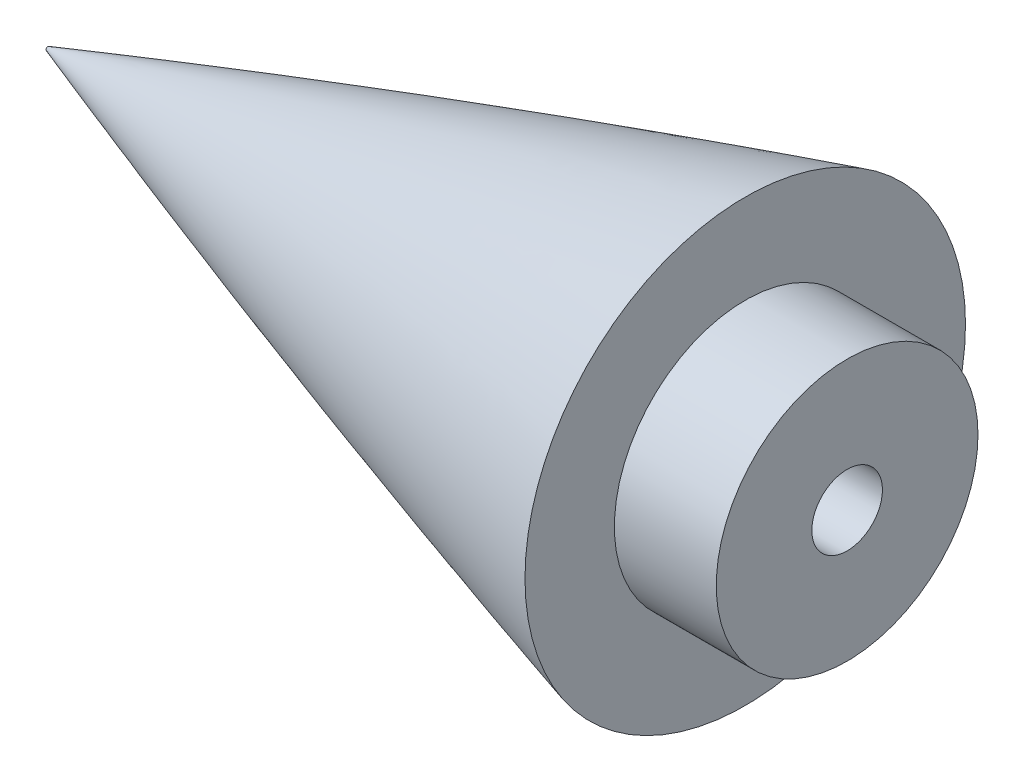
SolidWorks part; units mm, degrees
material "6061-T6 (SS)"
ref_plane "Front Plane" through (0, 0, 0) normal (0, 0, 1) x (1, 0, 0)
ref_plane "Top Plane" through (0, 0, 0) normal (0, 1, 0) x (1, 0, 0)
ref_plane "Right Plane" through (0, 0, 0) normal (1, 0, 0) x (0, 0, -1)
sketch "Sketch1" plane through (0, 0, 0) normal (0, 0, 1) x (1, 0, 0)
  line L0 (0, 0) -> (304.8, 0) construction
  line L1 (304.8, 0) -> (304.8, 51.1048) construction
  line L2 (304.8, 51.1048) -> (304.8, 0)
  line L3 (0, 0) -> (304.8, 0)
  spline S0 degree 9 poles (-29.1265, -10.5933) (11.3631, 4.8977) (51.8527, 17.9663) (92.3423, 28.7782) (132.8319, 37.4472) (173.3216, 44.0539) (213.8112, 48.652) (254.3008, 51.2735) (294.7904, 51.9289) (335.28, 50.6076) knots 0 0 0 0 0 0 0 0 0 0 1 1 1 1 1 1 1 1 1 1 construction
  spline S1 degree 9 poles (0, 0) (33.8667, 11.6851) (67.7333, 21.7357) (101.6, 30.2352) (135.4667, 37.2447) (169.3333, 42.8097) (203.2, 46.9625) (237.0667, 49.724) (270.9333, 51.1048) (304.8, 51.1048) knots 0.079929 0.079929 0.079929 0.079929 0.079929 0.079929 0.079929 0.079929 0.079929 0.079929 0.916357 0.916357 0.916357 0.916357 0.916357 0.916357 0.916357 0.916357 0.916357 0.916357
  point P0 (0, 0)
  dimension "D1" = 51.1048
revolve "Revolve1" add sketch "Sketch1" angle 360 about L3
sketch "Sketch2" plane through (0, 0, 0) normal (0, 0, 1) x (1, 0, 0)
  line L0 (304.8, -51.1048) -> (304.8, 51.1048) construction
  line L1 (50.8, -63.5) -> (317.5, -63.5)
  line L2 (50.8, -63.5) -> (50.8, 63.5)
  line L3 (50.8, 63.5) -> (317.5, 63.5)
  line L4 (317.5, -63.5) -> (317.5, 63.5)
  line L5 (50.8, -63.5) -> (317.5, 63.5) construction
  line L6 (50.8, 63.5) -> (317.5, -63.5) construction
  line L8 (-4.1425, 2.7598) -> (0.381, 2.7598)
  line L9 (-4.1425, 2.7598) -> (-4.1425, -2.7598)
  line L10 (-4.1425, -2.7598) -> (0.381, -2.7598)
  line L11 (0.381, 2.7598) -> (0.381, -2.7598)
  line L12 (-4.1425, 2.7598) -> (0.381, -2.7598) construction
  line L13 (-4.1425, -2.7598) -> (0.381, 2.7598) construction
  point P0 (184.15, 0)
  point P5 (0, 0)
  point P10 (-1.8807, 0)
  point P15 (0, 0)
  dimension "D1" = 50.8
  dimension "D2" = 127
  dimension "D3" = 12.7
  dimension "D4" = 0.381
extrude "Cut-Extrude1" cut sketch "Sketch2" against normal through all both and the other way through all
sketch "Sketch3" plane through (50.8, 0, 0) normal (1, 0, 0) x (0, 0, -1)
  circle A0 centre (0, 0) radius 9.4615
  dimension "D1" = 18.923
extrude "Boss-Extrude1" add sketch "Sketch3" along normal blind 7.366
hole_wizard "1/4-20 Tapped Hole1" positions "Sketch5" profile "Sketch6" tap size "1/4-20" standard "ANSI Inch"
sketch "Sketch5" plane through (58.166, 0, 0) normal (1, 0, 0) x (0, 0, -1)
  point P0 (0, 0)
sketch "Sketch6" plane through (58.166, 0, 0) normal (0, 1, 0) x (0, 0, -1)
  line L0 (0, 0) -> (0, 26.9338)
  line L1 (0, 26.9338) -> (2.5527, 25.4)
  line L2 (2.5527, 25.4) -> (2.5527, 0)
  line L5 (2.5527, 0) -> (0, 0)
  line L10 (0, 26.9338) -> (-2.5527, 25.4) construction
  line L11 (0, -6.35) -> (0, 107.95) construction
  dimension "Tap Drill Dia." = 5.1054
  dimension "Tap Drill Depth" = 25.4
  dimension "Drill Angle" = 118
cosmetic thread "Hole Thread1" parameters "D1"=12.7, "D2"=6.35
